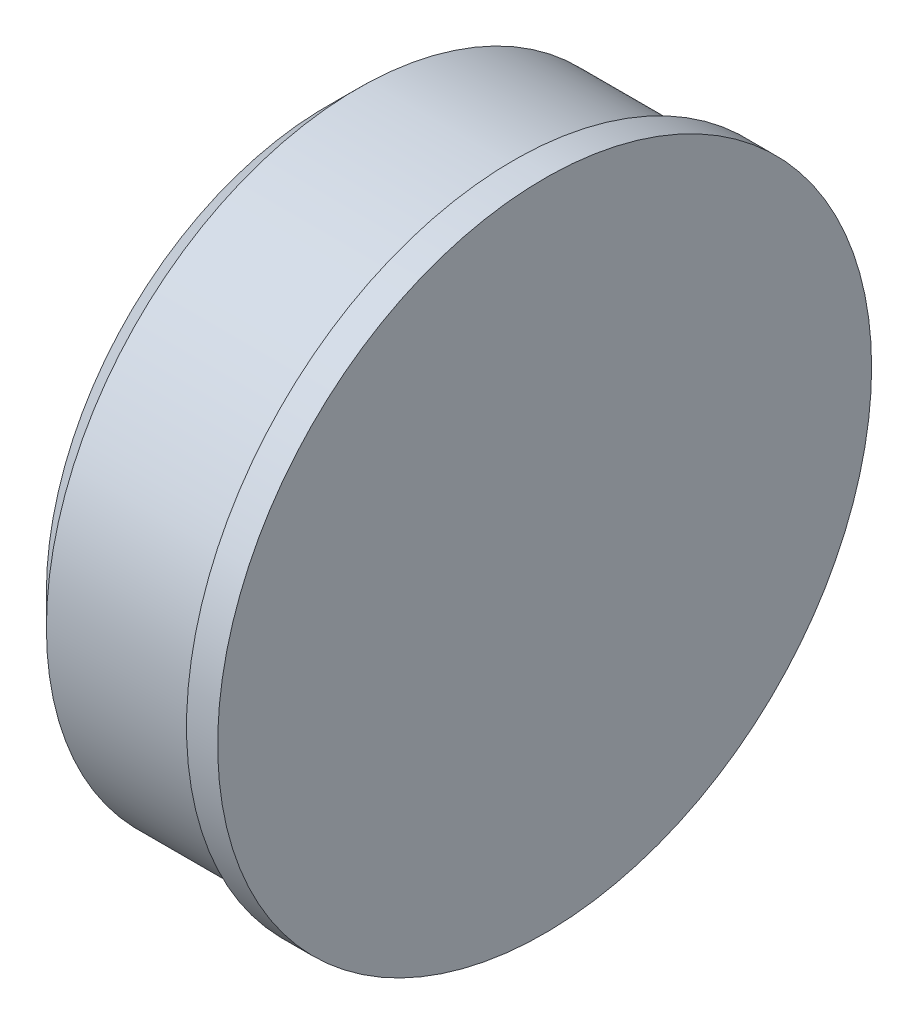
SolidWorks part; units mm, degrees
ref_plane "Plan de face" through (0, 0, 0) normal (0, 0, 1) x (1, 0, 0)
ref_plane "Plan de dessus" through (0, 0, 0) normal (0, 1, 0) x (1, 0, 0)
ref_plane "Plan de droite" through (0, 0, 0) normal (1, 0, 0) x (0, 0, -1)
sketch "Esquisse1" plane through (0, 0, 0) normal (1, 0, 0) x (0, 0, -1)
  circle A0 centre (0, 0) radius 10.5
  dimension "D1" = 21
extrude "Extrusion1" add sketch "Esquisse1" along normal blind 1
sketch "Esquisse2" plane through (0, 0, 0) normal (-1, 0, 0) x (0, 0, 1)
  circle A0 centre (0, 0) radius 10
  circle A1 centre (0, 0) radius 7.75
  dimension "D1" = 20
  dimension "D2" = 15.5
extrude "Extrusion2" add sketch "Esquisse2" along normal blind 6
chamfer "Chanfrein1" distance 1 angle 45 1 edges at (-6, 0, 10)
